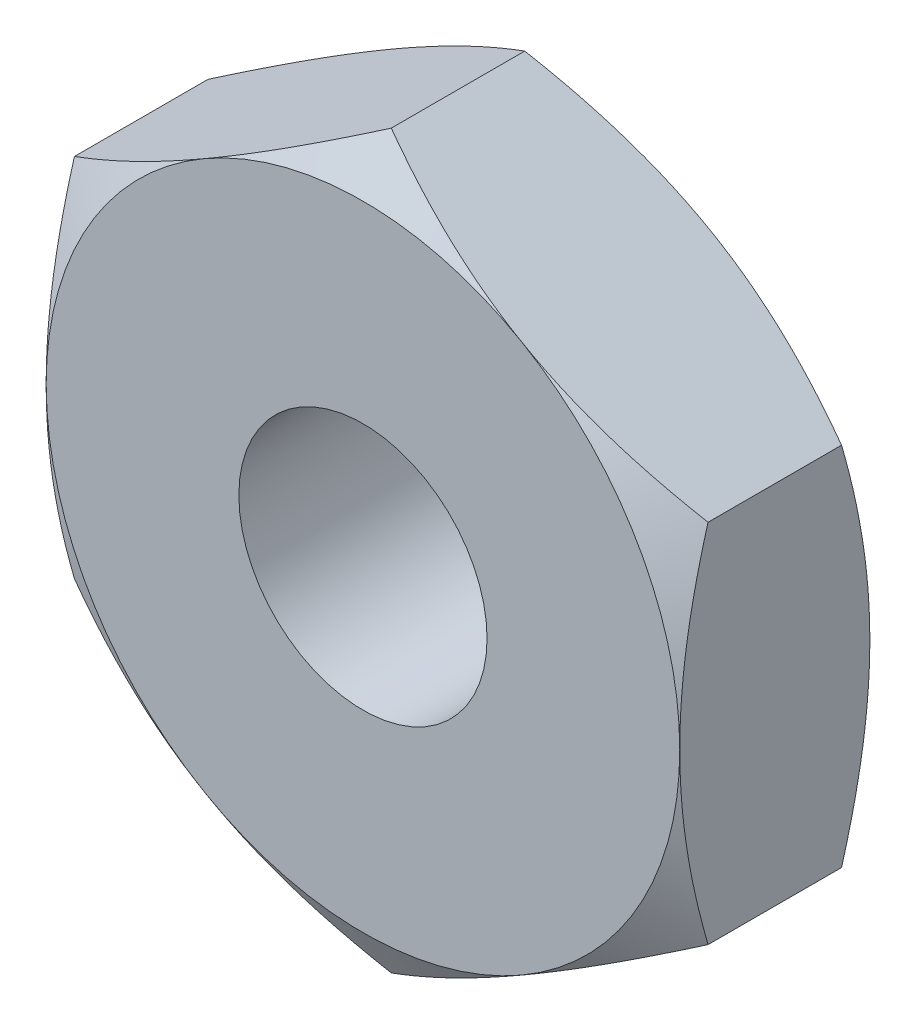
SolidWorks part; units mm, degrees
ref_plane "基准面1" through (0, 0, 0) normal (0, 0, 1) x (1, 0, 0)
ref_plane "基准面2" through (0, 0, 0) normal (0, 1, 0) x (1, 0, 0)
ref_plane "基准面3" through (0, 0, 0) normal (1, 0, 0) x (0, 0, -1)
sketch "尺寸草图" plane through (0, 0, 0) normal (0, 0, 1) x (1, 0, 0)
  line L0 (0, 0) -> (4.3, 0) construction
  line L1 (0, 0) -> (8.6, 0) construction
  line L2 (4.3, 0) -> (7.4, 0) construction
  line L3 (-1.9048, 0) -> (0, 0) construction
  point P3 (2, 0)
  point P4 (0.4, 0)
  point P5 (4.3, 0)
  point P6 (1.2, 0)
  point P8 (4, 0)
  dimension "D1" = 1.9048
  dimension "D" = 2
  dimension "P" = 0.4
  dimension "e(最小)" = 4.3
  dimension "m(最大)" = 1.2
  dimension "s(公称)" = 4
  dimension "dw(最小)" = 3.1
sketch "草图1" plane through (0, 0, 0) normal (0, 0, 1) x (1, 0, 0)
  line L0 (-2, 0) -> (2, 0) construction
  line L1 (0, 2.3094) -> (0, -2.3094) construction
  line L3 (0, 2.3094) -> (-2, 1.1547)
  line L4 (-2, 1.1547) -> (-2, -1.1547)
  line L5 (-2, -1.1547) -> (0, -2.3094)
  line L6 (0, -2.3094) -> (2, -1.1547)
  line L7 (2, -1.1547) -> (2, 1.1547)
  line L8 (2, 1.1547) -> (0, 2.3094)
  circle A0 centre (0, 0) radius 2 construction
  circle A1 centre (0, 0) radius 0.7835
  point P2 (0, 1.9906)
  dimension "D1" = 4.3
  dimension "D" = 1.567
  dimension "D2" = 4
extrude "基体-拉伸" add sketch "草图1" along normal blind 1.2
cosmetic thread "装饰螺纹线1" parameters "D2"=2
sketch "草图2" plane through (0, 0, 0) normal (0, 0, -1) x (-1, 0, 0)
  circle A0 centre (0, 0) radius 2
  circle A1 centre (0, 0) radius 0.7835 construction
  dimension "s" = 4
extrude "切除-拉伸1" cut sketch "草图2" against normal through all draft 60 flip side to cut
sketch "草图3" plane through (0, 0, 1.2) normal (0, 0, 1) x (1, 0, 0)
  circle A0 centre (0, 0) radius 2
  dimension "D1" = 4
extrude "切除-拉伸2" cut sketch "草图3" against normal through all draft 60 flip side to cut
